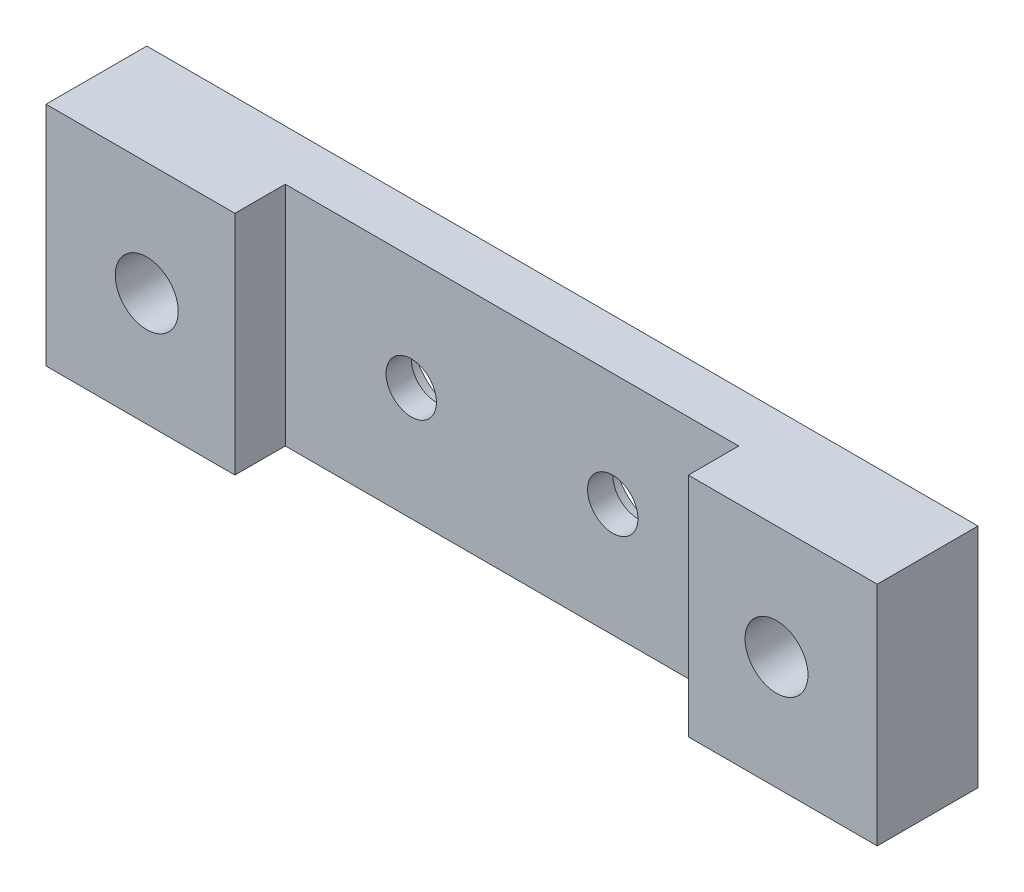
SolidWorks part; units mm, degrees
ref_plane "Front Plane" through (0, 0, 0) normal (0, 0, 1) x (1, 0, 0)
ref_plane "Top Plane" through (0, 0, 0) normal (0, 1, 0) x (1, 0, 0)
ref_plane "Right Plane" through (0, 0, 0) normal (1, 0, 0) x (0, 0, -1)
sketch "Sketch1" plane through (0, 0, 0) normal (0, 1, 0) x (1, 0, 0)
  line L0 (-52.3875, 0) -> (52.3875, 0)
  line L1 (52.3875, 0) -> (52.3875, -12.7)
  line L2 (52.3875, -12.7) -> (28.575, -12.7)
  line L3 (28.575, -12.7) -> (28.575, -6.35)
  line L4 (28.575, -6.35) -> (-28.575, -6.35)
  line L5 (-28.575, -6.35) -> (-28.575, -12.7)
  line L6 (-28.575, -12.7) -> (-52.3875, -12.7)
  line L7 (-52.3875, -12.7) -> (-52.3875, 0)
  point P7 (0, 0)
  point P10 (0, -6.35)
  dimension "D1" = 104.775
  dimension "D2" = 12.7
  dimension "D3" = 57.15
  dimension "D4" = 6.35
extrude "Boss-Extrude1" add sketch "Sketch1" along normal blind 28.575
hole_wizard "Hole1" positions "Sketch2" profile "Sketch3" legacy end condition through all
sketch "Sketch2" plane through (0, 0, 0) normal (0, 0, -1) x (-1, 0, 0)
  line L0 (-12.7, 14.2875) -> (12.7, 14.2875) construction
  line L2 (-52.3875, 28.575) -> (-52.3875, 0) construction
  point P0 (-12.7, 14.2875)
  point P2 (12.7, 14.2875)
  point P13 (0, 14.2875)
  point P18 (-52.3875, 14.2875)
  dimension "D1" = 25.4
sketch "Sketch3" plane through (12.7, 14.2875, 0) normal (1, 0, 0) x (0, 1, 0)
  line L0 (0, 0) -> (0, 14.6077)
  line L1 (0, 14.6077) -> (3.175, 12.7)
  line L2 (3.175, 12.7) -> (3.175, 3.175)
  line L3 (3.175, 3.175) -> (6.35, 3.175)
  line L4 (6.35, 0) -> (0, 0)
  line L5 (0, -11.3109) -> (0, 121.1557) construction
  line L6 (0, 14.6077) -> (-3.175, 12.7) construction
  line L7 (6.35, 3.175) -> (6.35, 0)
  dimension "Depth" = 12.7
  dimension "Drill Angle" = 118
  dimension "Diameter" = 6.35
  dimension "C-Bore Diameter" = 12.7
  dimension "C-Bore Depth" = 3.175
hole_wizard "5/16 (0.3125) Diameter Hole1" positions "Sketch6" profile "Sketch5" hole size "5/16" standard "ANSI Inch" end condition through all
sketch "Sketch6" plane through (0, 0, 12.7) normal (0, 0, 1) x (1, 0, 0)
  line L0 (-52.3875, 28.575) -> (-52.3875, 0) construction
  line L3 (52.3875, 28.575) -> (52.3875, 0) construction
  line L4 (-28.575, 28.575) -> (28.575, 28.575) construction
  point P0 (-39.6875, 14.2875)
  point P2 (39.6875, 14.2875)
  point P8 (-52.3875, 14.2875)
  point P20 (52.3875, 14.2875)
  point P23 (0, 28.575)
  dimension "D1" = 79.375
  dimension "D2" = 39.6875
sketch "Sketch5" plane through (-39.6875, 14.2875, 12.7) normal (1, 0, 0) x (0, -1, 0)
  line L0 (0, 0) -> (0, 12.7)
  line L1 (0, 12.7) -> (3.9687, 12.7)
  line L2 (3.9687, 12.7) -> (3.9687, 0)
  line L5 (3.9687, 0) -> (0, 0)
  line L11 (0, -6.35) -> (0, 107.95) construction
  dimension "Thru Hole Dia." = 7.9375
  dimension "Thru Hole Depth" = 12.7
equation "\"D2@Sketch6\"=\"D1@Sketch6\"/2"
